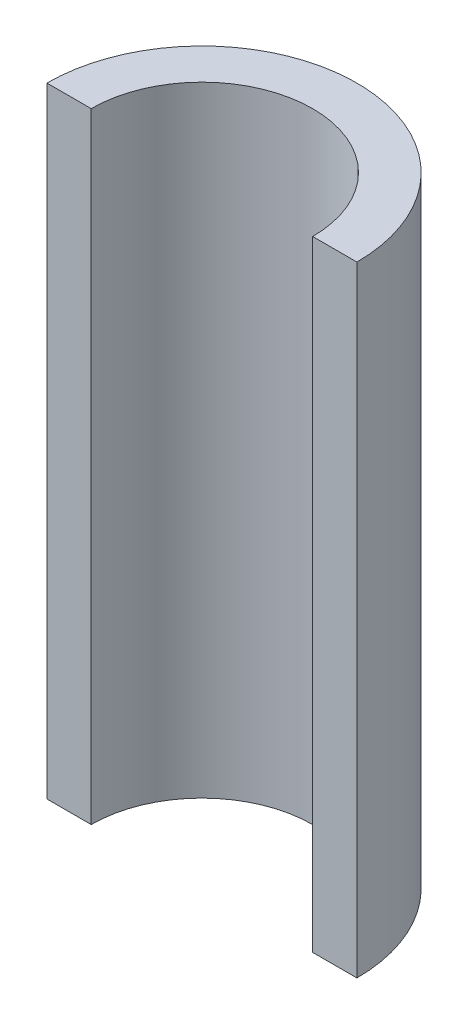
SolidWorks part; units mm, degrees
ref_plane "Front Plane" through (0, 0, 0) normal (0, 0, 1) x (1, 0, 0)
ref_plane "Top Plane" through (0, 0, 0) normal (0, 1, 0) x (1, 0, 0)
ref_plane "Right Plane" through (0, 0, 0) normal (1, 0, 0) x (0, 0, -1)
sketch "Sketch1" plane through (0, 0, 0) normal (0, 1, 0) x (1, 0, 0)
  line L0 (-17.5, 0) -> (-12.5, 0)
  line L1 (12.5, 0) -> (17.5, 0)
  arc A0 (12.5, 0) -> (-12.5, 0) centre (0, 0) ccw
  arc A1 (17.5, 0) -> (-17.5, 0) centre (0, 0) ccw
  dimension "D1" = 25
  dimension "D2" = 35
extrude "Boss-Extrude1" add sketch "Sketch1" along normal blind 70
